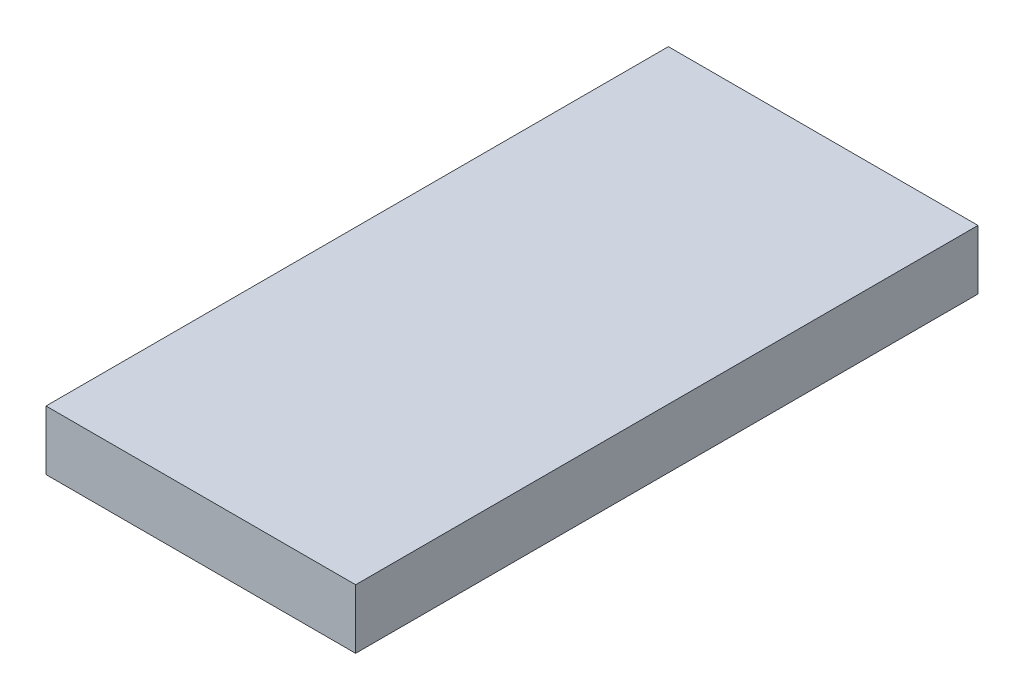
SolidWorks part; units mm, degrees
ref_plane "Front Plane" through (0, 0, 0) normal (0, 0, 1) x (1, 0, 0)
ref_plane "Top Plane" through (0, 0, 0) normal (0, 1, 0) x (1, 0, 0)
ref_plane "Right Plane" through (0, 0, 0) normal (1, 0, 0) x (0, 0, -1)
sketch "Sketch1" plane through (0, 0, 0) normal (0, 1, 0) x (1, 0, 0)
  line L1 (-6.2865, 12.6365) -> (6.2865, 12.6365)
  line L2 (-6.2865, 12.6365) -> (-6.2865, -12.6365)
  line L3 (-6.2865, -12.6365) -> (6.2865, -12.6365)
  line L4 (6.2865, 12.6365) -> (6.2865, -12.6365)
  line L5 (-6.2865, 12.6365) -> (6.2865, -12.6365) construction
  line L6 (-6.2865, -12.6365) -> (6.2865, 12.6365) construction
  point P0 (0, 0)
  dimension "D1" = 25.273
  dimension "D2" = 12.573
extrude "Boss-Extrude1" add sketch "Sketch1" along normal blind 2.413
